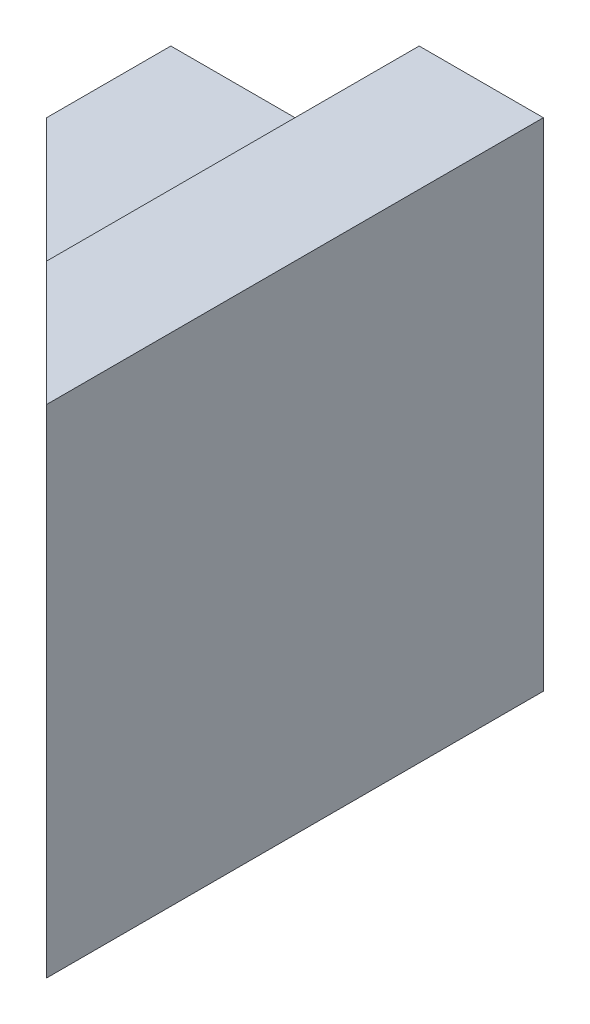
SolidWorks part; units mm, degrees
ref_plane "Front" through (0, 0, 0) normal (0, 0, 1) x (1, 0, 0)
ref_plane "Top" through (0, 0, 0) normal (0, 1, 0) x (1, 0, 0)
ref_plane "Right" through (0, 0, 0) normal (1, 0, 0) x (0, 0, -1)
sketch "Sketch1" plane through (0, 0, 0) normal (0, 0, 1) x (1, 0, 0)
  line L0 (0, 0) -> (0, 2)
  line L1 (0, 2) -> (1, 2)
  line L2 (1, 2) -> (1, 3)
  line L3 (1, 3) -> (3, 3)
  line L4 (3, 3) -> (3, 4)
  line L5 (3, 4) -> (4, 4)
  line L6 (4, 4) -> (4, 0)
  line L7 (4, 0) -> (3, 0)
  line L8 (3, 0) -> (3, 1)
  line L9 (3, 1) -> (1, 1)
  line L10 (1, 1) -> (1, 0)
  line L11 (1, 0) -> (0, 0)
  dimension "D1" = 4
  dimension "D2" = 1
  dimension "D3" = 1
  dimension "D4" = 1
  dimension "D5" = 1
  dimension "D6" = 2
  dimension "D7" = 1
  dimension "D8" = 1
  dimension "D9" = 2
extrude "Boss-Extrude1" add sketch "Sketch1" along normal blind 4
sketch "Sketch2" plane through (0, 4, 0) normal (0, 1, 0) x (1, 0, 0)
  line L0 (0, 0) -> (4, -4)
  line L1 (4, -4) -> (0, -4)
  line L2 (0, -4) -> (0, 0)
extrude "Cut-Extrude1" cut sketch "Sketch2" against normal blind 10
